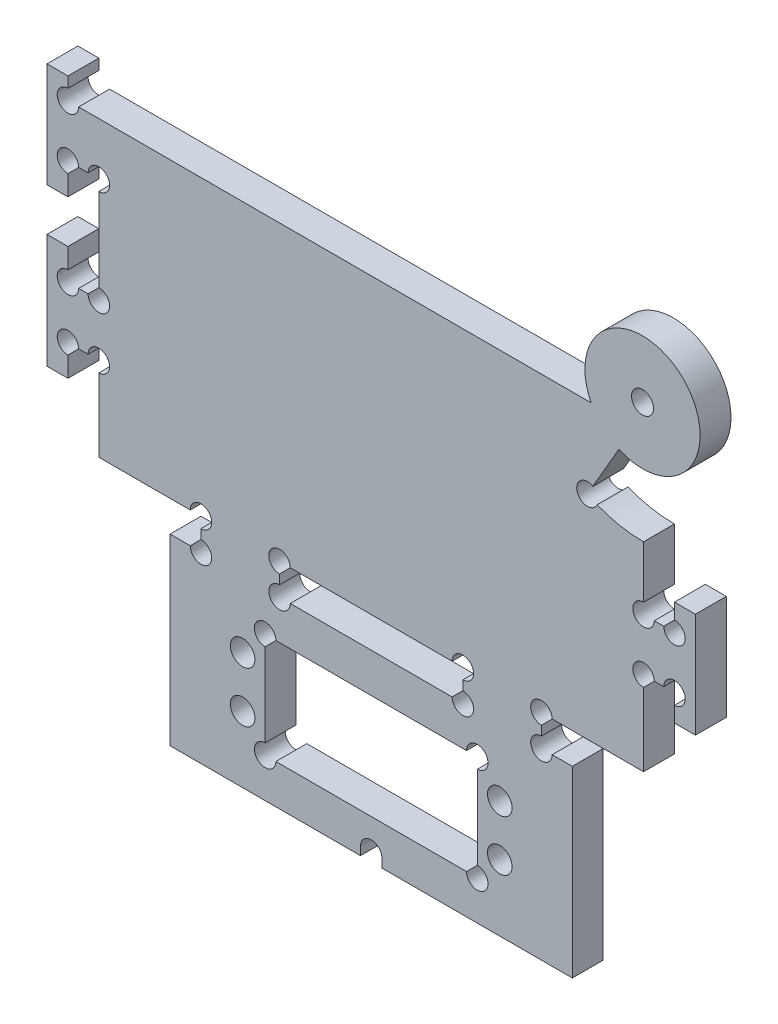
SolidWorks part; units mm, degrees
other "Markup1"
sketch "Sketch13" plane through (62.7989, -73.1, 0) normal (0.9574, -0.0867, -0.2756) x (-0.2697, 0.0736, -0.9601)
ref_plane "Front Plane" through (0, 0, 0) normal (0, 0, 1) x (1, 0, 0)
ref_plane "Top Plane" through (0, 0, 0) normal (0, 1, 0) x (1, 0, 0)
ref_plane "Right Plane" through (0, 0, 0) normal (1, 0, 0) x (0, 0, -1)
sketch "Sketch2" plane through (0, 0, 0) normal (0, 0, 1) x (1, 0, 0)
  line L1 (52, -33) -> (-52, -33)
  line L2 (52, -33) -> (52, 33)
  line L3 (52, 33) -> (-52, 33)
  line L4 (-52, -33) -> (-52, 33)
  line L5 (52, -33) -> (-52, 33) construction
  line L6 (52, 33) -> (-52, -33) construction
  point P0 (0, 0)
  dimension "D1" = 104
  dimension "D2" = 66
extrude "Boss-Extrude1" add sketch "Sketch2" along normal blind 5.9
sketch "Sketch3" plane through (0, 0, 5.9) normal (0, 0, 1) x (1, 0, 0)
  line L0 (-52, -17) -> (-57.9, -17)
  line L1 (-52, 33) -> (-52, -33) construction
  line L2 (-57.9, -17) -> (-57.9, -22.9)
  line L3 (-57.9, -22.9) -> (-61.9, -22.9)
  line L4 (-61.9, -22.9) -> (-61.9, -1.1)
  line L5 (-61.9, -1.1) -> (-57.9, -1.1)
  line L6 (-57.9, -1.1) -> (-57.9, -7)
  line L7 (-57.9, -7) -> (-52, -7)
  line L8 (-52, -7) -> (-52, -17) construction
  line L9 (-52, -7) -> (-52, -17)
  line L10 (-52, -33) -> (52, -33) construction
  line L11 (-52, 13) -> (-57.9, 13)
  line L12 (-52, 23) -> (-52, 13)
  line L13 (-57.9, 23) -> (-52, 23)
  line L14 (-57.9, 27.1) -> (-57.9, 23)
  line L15 (-61.9, 27.1) -> (-57.9, 27.1)
  line L16 (-61.9, 7.1) -> (-61.9, 27.1)
  line L17 (-57.9, 7.1) -> (-61.9, 7.1)
  line L18 (-57.9, 13) -> (-57.9, 7.1)
  line L19 (0, 0) -> (0, -19.6599) construction
  line L20 (52, -7) -> (52, -17) construction
  line L21 (52, -7) -> (52, -17)
  line L22 (57.9, -7) -> (52, -7)
  line L23 (57.9, -2) -> (57.9, -7)
  line L24 (61.9, -2) -> (57.9, -2)
  line L25 (61.9, -22) -> (61.9, -2)
  line L26 (57.9, -22) -> (61.9, -22)
  line L27 (57.9, -17) -> (57.9, -22)
  line L28 (52, -17) -> (57.9, -17)
  line L29 (-32.5, -33) -> (-32.5, -38.9)
  line L30 (-32.5, -38.9) -> (-38.4, -38.9)
  line L31 (-38.4, -38.9) -> (-38.4, -73.9)
  line L34 (17.5, -38.9) -> (-17.5, -38.9)
  line L35 (-17.5, -38.9) -> (-17.5, -33)
  line L36 (-17.5, -33) -> (-32.5, -33)
  line L45 (-17.5, -33) -> (17.5, -33) construction
  line L46 (-38.4, -73.9) -> (38.4, -73.9)
  line L47 (17.5, -33) -> (32.5, -33)
  line L48 (17.5, -38.9) -> (17.5, -33)
  line L49 (38.4, -38.9) -> (38.4, -73.9)
  line L50 (32.5, -38.9) -> (38.4, -38.9)
  line L51 (32.5, -33) -> (32.5, -38.9)
  line L52 (52, 33) -> (-52, 33) construction
  line L53 (52, -33) -> (52, 33) construction
  point P4 (-61.9, -12)
  point P11 (-52, -12)
  point P44 (0, -33)
  point P46 (0, -73.9)
  point P48 (0, -38.9)
  dimension "D3" = 5.9
  dimension "D6" = 4
  dimension "D8" = 15
  dimension "D10" = 5.9
  dimension "D11" = 35
  dimension "D12" = 17.5
  dimension "D9" = 5.9
  dimension "D13" = 5.9
  dimension "D14" = 10
  dimension "D4" = 10
  dimension "D5" = 20
  dimension "D2" = 20
  dimension "D7" = 10
  dimension "D16" = 5.9
  dimension "D18" = 5.9
  dimension "D19" = 4
  dimension "Accident" = 5.9
  dimension "D21" = 10
  dimension "D22" = 20
  dimension "D23" = 11
  dimension "D15" = 4
extrude "Boss-Extrude2" add sketch "Sketch3" against normal through all
sketch "Sketch4" plane through (0, 0, 5.9) normal (0, 0, 1) x (1, 0, 0)
  line L0 (52, -7) -> (52, 33) construction
  line L1 (-52, 33) -> (52, 33)
  line L2 (-52, 33) -> (-52, 23)
  line L3 (-52, 23) -> (52, 23)
  line L4 (52, 33) -> (52, 23)
  dimension "D1" = 10
extrude "Cut-Extrude1" cut sketch "Sketch4" against normal blind 8
sketch "Sketch6" plane through (0, 0, 5.9) normal (0, 0, 1) x (1, 0, 0)
  line L0 (-57.9, 23) -> (52, 23) construction
  line L1 (52, -7) -> (52, 23) construction
  line L2 (52, 17) -> (52, 0)
  line L3 (52, 0) -> (0, 0)
  line L4 (0, 0) -> (0, 23)
  line L5 (0, 23) -> (42, 23)
  line L6 (52, -7) -> (52, 23) construction
  line L7 (52, 23) -> (-57.9, 23) construction
  arc A0 (42, 23) -> (52, 17) centre (51.7989, 27.9982) cw
  dimension "D1" = 10
  dimension "D2" = 6
extrude "Boss-Extrude4" add sketch "Sketch6" against normal up to surface (5.9 mm away) up to face at (-10.4529, -14.3235, 0)
sketch "Sketch8" plane through (0, 0, 5.9) normal (0, 0, 1) x (1, 0, 0)
  line L1 (47.2877, 17.9658) -> (41.2877, 7.5735)
  line L2 (52, 17) -> (52, 5.0283)
  line L3 (52, -7) -> (52, 17) construction
  arc A3 (41.2877, 7.5735) -> (52, 5.0283) centre (51.7989, 27.9982) ccw
  arc A4 (47.2877, 17.9658) -> (52, 17) centre (51.7989, 27.9982) ccw
  arc A5 (52, 17) -> (42, 23) centre (51.7989, 27.9982) ccw construction
  dimension "D2" = 30
  dimension "D1" = 12
extrude "Cut-Extrude2" cut sketch "Sketch8" against normal blind 8
sketch "Sketch9" plane through (0, 0, 5.9) normal (0, 0, 1) x (1, 0, 0)
  line L5 (53.5273, 29.191) -> (50.0705, 26.8054) construction
  arc A0 (47.2877, 17.9658) -> (42, 23) centre (51.7989, 27.9982) ccw construction
  circle A1 centre (51.7989, 27.9982) radius 2.1
  point P0 (51.7989, 27.9982)
  dimension "D1" = 4.2
extrude "Cut-Extrude3" cut sketch "Sketch9" against normal through all
sketch "Sketch10" plane through (0, 0, 5.9) normal (0, 0, 1) x (1, 0, 0)
  line L0 (-24.55, -56.4) -> (-38.4, -56.4) construction
  line L9 (-24.55, -51.55) -> (24.55, -51.55) construction
  line L10 (-24.55, -51.55) -> (-24.55, -61.25) construction
  line L11 (-24.55, -61.25) -> (24.55, -61.25) construction
  line L13 (24.55, -51.55) -> (24.55, -61.25) construction
  line L14 (-24.55, -51.55) -> (24.55, -61.25) construction
  line L15 (-24.55, -61.25) -> (24.55, -51.55) construction
  line L16 (0, -51.55) -> (0, -46.0939) construction
  line L17 (-20.25, -46.4) -> (20.25, -46.4)
  line L18 (-20.25, -46.4) -> (-20.25, -66.4)
  line L19 (-20.25, -66.4) -> (20.25, -66.4)
  line L20 (-38.4, -38.9) -> (38.4, -38.9) construction
  line L21 (-38.4, -38.9) -> (-38.4, -73.9) construction
  line L22 (20.25, -46.4) -> (20.25, -66.4)
  line L23 (-20.25, -46.4) -> (20.25, -66.4) construction
  line L24 (-20.25, -66.4) -> (20.25, -46.4) construction
  line L25 (0, -46.0939) -> (0, -38.9) construction
  line L26 (17.5, -38.9) -> (-17.5, -38.9) construction
  line L27 (-38.4, -38.9) -> (-38.4, -73.9) construction
  line L28 (-38.4, -73.9) -> (38.4, -73.9) construction
  line L29 (38.4, -38.9) -> (38.4, -73.9) construction
  line L30 (-38.4, -38.9) -> (38.4, -73.9) construction
  line L31 (-38.4, -73.9) -> (38.4, -38.9) construction
  circle A8 centre (-24.55, -51.55) radius 2.35
  circle A9 centre (-24.55, -61.25) radius 2.35
  circle A10 centre (24.55, -61.25) radius 2.35
  circle A11 centre (24.55, -51.55) radius 2.35
  point P0 (-24.55, -51.55)
  point P1 (-24.55, -61.25)
  point P3 (24.55, -61.25)
  point P5 (24.55, -51.55)
  point P11 (0, -56.4)
  point P23 (0, -56.4)
  point P31 (0, -56.4)
  dimension "D3" = 4.7
  dimension "D1" = 49.1
  dimension "D2" = 9.7
  dimension "D4" = 40.5
  dimension "D5" = 20
extrude "Cut-Extrude4" cut sketch "Sketch10" against normal up to next
sketch "Sketch11" plane through (0, 0, 5.9) normal (0, 0, 1) x (1, 0, 0)
  circle A0 centre (-52, 13) radius 2.05
  circle A1 centre (-52, -7) radius 2.05
  circle A2 centre (-57.9, -7) radius 2.05
  circle A3 centre (-57.9, 13) radius 2.05
  circle A4 centre (-57.9, 23) radius 2.05
  circle A5 centre (-52, -17) radius 2.05
  circle A6 centre (-57.9, -17) radius 2.05
  circle A7 centre (-32.5, -38.9) radius 2.05
  circle A8 centre (-32.5, -33) radius 2.05
  circle A9 centre (-17.5, -33) radius 2.05
  circle A10 centre (-17.5, -38.9) radius 2.05
  circle A11 centre (17.5, -33) radius 2.05
  circle A12 centre (17.5, -38.9) radius 2.05
  circle A13 centre (32.5, -33) radius 2.05
  circle A14 centre (32.5, -38.9) radius 2.05
  circle A15 centre (-20.25, -46.4) radius 2.05
  circle A16 centre (-20.25, -66.4) radius 2.05
  circle A17 centre (20.25, -66.4) radius 2.05
  circle A18 centre (20.25, -46.4) radius 2.05
  circle A19 centre (52, -17) radius 2.05
  circle A20 centre (57.9, -17) radius 2.05
  circle A21 centre (57.9, -7) radius 2.05
  circle A22 centre (52, -7) radius 2.05
  circle A23 centre (41.2877, 7.5735) radius 2.05
  dimension "D1" = 4.1
extrude "Cut-Extrude5" cut sketch "Sketch11" against normal up to next
sketch "Sketch12" plane through (0, 0, 5.9) normal (0, 0, 1) x (1, 0, 0)
  line L0 (0, -66.4) -> (0, -73.9) construction
  line L2 (-38.4, -73.9) -> (38.4, -73.9) construction
  line L3 (-18.2, -66.4) -> (18.2, -66.4) construction
  line L4 (-2.05, -72.3) -> (-2.05, -73.9)
  line L5 (2.05, -72.3) -> (2.05, -73.9)
  line L6 (2.05, -73.9) -> (-2.05, -73.9)
  circle A0 centre (0, -72.3) radius 2.05 construction
  arc A1 (-2.05, -72.3) -> (2.05, -72.3) centre (0, -72.3) cw
  dimension "D1" = 4.1
  dimension "D2" = 5.9
extrude "Cut-Extrude6" cut sketch "Sketch12" against normal up to next
equation "\"D1@Boss-Extrude1\"=\"e\""
equation "\"e\" = 5.9"
equation "\"D3@Sketch3\"= \"e\""
equation "\"D10@Sketch3\"= \"e\""
equation "\"D9@Sketch3\"= \"e\""
equation "\"D13@Sketch3\"= \"e\""
equation "\"D16@Sketch3\"= \"e\""
equation "\"D18@Sketch3\"= \"e\""
equation "\"Accident@Sketch3\"= \"e\""
equation "\"D2@Sketch12\"= \"e\""
